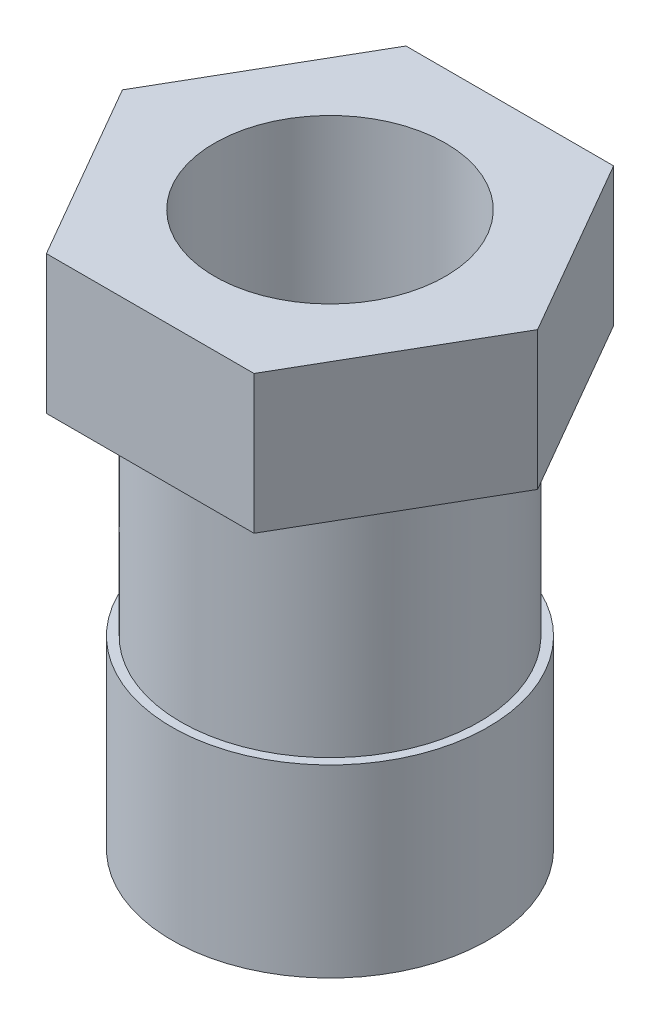
SolidWorks part; units mm, degrees
ref_plane "Alzado" through (0, 0, 0) normal (0, 0, 1) x (1, 0, 0)
ref_plane "Planta" through (0, 0, 0) normal (0, 1, 0) x (1, 0, 0)
ref_plane "Vista lateral" through (0, 0, 0) normal (1, 0, 0) x (0, 0, -1)
sketch "Croquis1" plane through (0, 0, 0) normal (0, 1, 0) x (1, 0, 0)
  line L1 (22.5, 0) -> (11.25, 19.4856)
  line L2 (11.25, 19.4856) -> (-11.25, 19.4856)
  line L3 (-11.25, 19.4856) -> (-22.5, 0)
  line L4 (-22.5, 0) -> (-11.25, -19.4856)
  line L5 (-11.25, -19.4856) -> (11.25, -19.4856)
  line L6 (11.25, -19.4856) -> (22.5, 0)
  circle A0 centre (0, 0) radius 19.4856 construction
  dimension "D1" = 45
extrude "Saliente-Extruir1" add sketch "Croquis1" along normal blind 15
sketch "Croquis2" plane through (0, 0, 0) normal (0, -1, 0) x (1, 0, 0)
  circle A0 centre (0, 0) radius 16.164
extrude "Saliente-Extruir2" add sketch "Croquis2" along normal blind 25
sketch "Croquis3" plane through (0, -25, 0) normal (0, -1, 0) x (1, 0, 0)
  circle A0 centre (0, 0) radius 17.1342
extrude "Saliente-Extruir3" add sketch "Croquis3" along normal blind 20
sketch "Croquis4" plane through (0, -45, 0) normal (0, -1, 0) x (1, 0, 0)
  circle A0 centre (0, 0) radius 12.5141
extrude "Cortar-Extruir1" cut sketch "Croquis4" against normal through all
